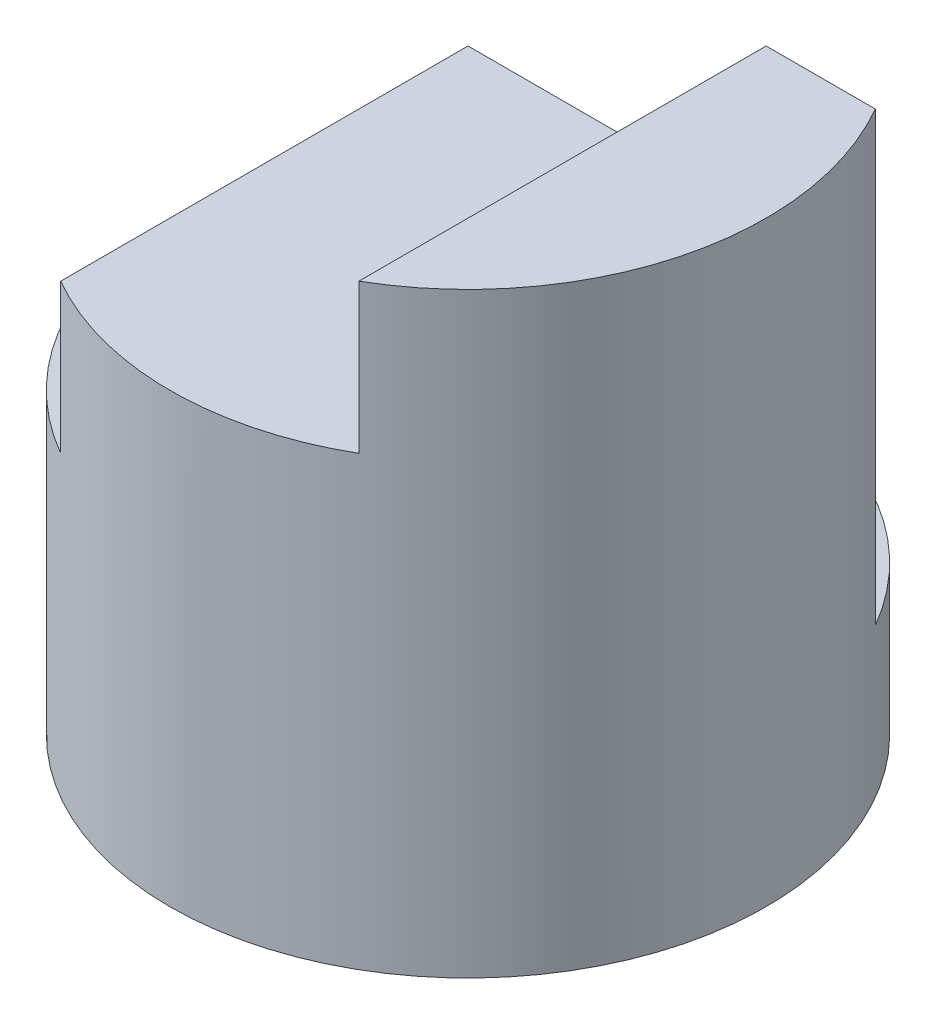
SolidWorks part; units mm, degrees
ref_plane "Front" through (0, 0, 0) normal (0, 0, 1) x (1, 0, 0)
ref_plane "Top" through (0, 0, 0) normal (0, 1, 0) x (1, 0, 0)
ref_plane "Right" through (0, 0, 0) normal (1, 0, 0) x (0, 0, -1)
sketch "Sketch1" plane through (0, 0, 0) normal (0, 1, 0) x (1, 0, 0)
  circle A0 centre (0, 0) radius 2
  dimension "D1" = 4
extrude "Boss-Extrude1" add sketch "Sketch1" along normal blind 4
sketch "Sketch2" plane through (0, 0, 0) normal (0, 0, 1) x (1, 0, 0)
  line L0 (1, 4) -> (1, 3)
  line L1 (2, 4) -> (-2, 4) construction
  line L2 (1, 3) -> (-1, 3)
  line L3 (-1, 3) -> (-1, 2)
  line L4 (-1, 2) -> (-2, 2)
  line L5 (-2, 4) -> (-2, 0) construction
  line L6 (-2, 2) -> (-2, 4)
  line L7 (-2, 4) -> (1, 4)
  dimension "D1" = 1
  dimension "D2" = 1
  dimension "D3" = 2
  dimension "D4" = 1
extrude "Cut-Extrude1" cut sketch "Sketch2" against normal mid plane 4
sketch "Sketch3" plane through (0, 4, 0) normal (0, 1, 0) x (1, 0, 0)
  line L0 (-1.7321, 1) -> (1.7321, 1)
  arc A0 (-1, 1.7321) -> (-1, -1.7321) centre (0, 0) ccw construction
  arc A1 (1, -1.7321) -> (1, 1.7321) centre (0, 0) ccw construction
  arc A2 (-1.7321, 1) -> (1.7321, 1) centre (0, 0) cw
  dimension "D1" = 1
extrude "Cut-Extrude2" cut sketch "Sketch3" against normal blind 3
